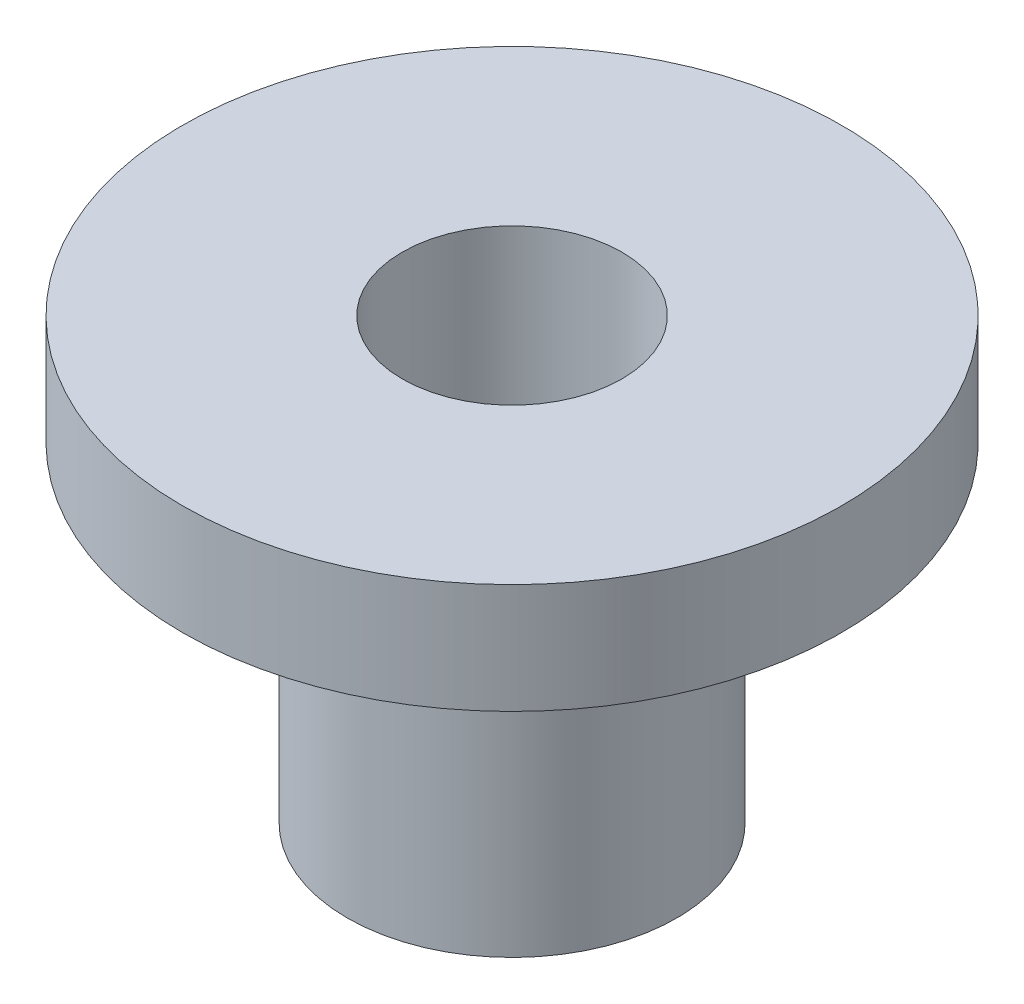
SolidWorks part; units mm, degrees
material "Rubber"
ref_plane "Front Plane" through (0, 0, 0) normal (0, 0, 1) x (1, 0, 0)
ref_plane "Top Plane" through (0, 0, 0) normal (0, 1, 0) x (1, 0, 0)
ref_plane "Right Plane" through (0, 0, 0) normal (1, 0, 0) x (0, 0, -1)
sketch "Sketch1" plane through (0, 0, 0) normal (0, 0, 1) x (1, 0, 0)
  line L0 (0, 0) -> (0, -12.7) construction
  line L1 (0, -55) -> (0, 55) construction
  line L2 (55, 0) -> (-55, 0) construction
  line L3 (-9.525, 0) -> (-3.175, 0)
  line L4 (-9.525, 0) -> (-9.525, -3.175)
  line L5 (-9.525, -3.175) -> (-4.7625, -3.175)
  line L6 (-3.175, 0) -> (-3.175, -12.7)
  line L8 (-4.7625, -3.175) -> (-4.7625, -12.7)
  line L9 (-4.7625, -12.7) -> (-3.175, -12.7)
  dimension "D1" = 6.35
  dimension "D2" = 12.7
  dimension "D3" = 3.175
  dimension "D4" = 1.5875
  dimension "D5" = 19.05
revolve "Revolve1" add sketch "Sketch1" angle 360 about L0
